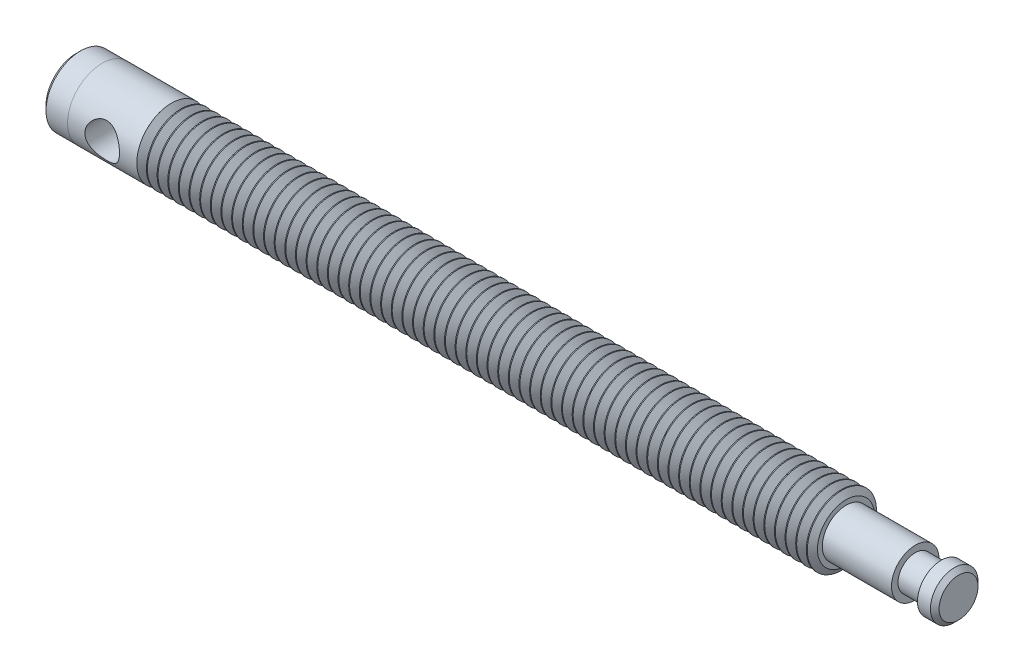
SolidWorks part; units mm, degrees
material "AISI 1015 Steel, Cold Drawn (SS)"
ref_plane "Front Plane" through (0, 0, 0) normal (0, 0, 1) x (1, 0, 0)
ref_plane "Top Plane" through (0, 0, 0) normal (0, 1, 0) x (1, 0, 0)
ref_plane "Right Plane" through (0, 0, 0) normal (1, 0, 0) x (0, 0, -1)
sketch "Sketch1" plane through (0, 0, 0) normal (1, 0, 0) x (0, 0, -1)
  circle A0 centre (0, 0) radius 6.35
  dimension "D1" = 12.7
extrude "Extrude1" add sketch "Sketch1" along normal blind 123.825
sketch "Sketch2" plane through (0, 0, 0) normal (0, 0, 1) x (1, 0, 0)
  line L0 (-0.0003, 6.35) -> (0.889, 5.08)
  line L1 (0.889, 5.08) -> (1.7783, 6.35)
  line L2 (1.7783, 6.35) -> (1.7783, 7.9375)
  line L3 (1.7783, 7.9375) -> (-0.0003, 7.9375)
  line L4 (-0.0003, 7.9375) -> (-0.0003, 6.35)
  line L5 (123.825, 0) -> (0, 0) construction
  line L6 (0, 0) -> (50.8, 0) construction
  dimension "D1" = 55
  dimension "D2" = 70
  dimension "D3" = 15.875
  dimension "D4" = 1.27
  dimension "D5" = 12.7
  dimension "D6" = 0.889
revolve "Cut-Revolve1" cut sketch "Sketch2" angle 360 about L6
pattern_linear "LPattern2" count 64 spacing 1.9533 along (1, 0, 0) of "Cut-Revolve1"
sketch "Sketch3" plane through (123.825, 0, 0) normal (1, 0, 0) x (0, 0, -1)
  circle A0 centre (0, 0) radius 4.3656
  dimension "D1" = 8.7312
extrude "Extrude2" add sketch "Sketch3" along normal blind 12.7
sketch "Sketch4" plane through (136.525, 0, 0) normal (1, 0, 0) x (0, 0, -1)
  circle A0 centre (0, 0) radius 3.175
  dimension "D1" = 6.35
extrude "Extrude3" add sketch "Sketch4" along normal blind 4.7625
sketch "Sketch5" plane through (141.2875, 0, 0) normal (1, 0, 0) x (0, 0, -1)
  circle A0 centre (0, 0) radius 4.3656
  dimension "D1" = 8.7312
extrude "Extrude4" add sketch "Sketch5" along normal blind 3.175
chamfer "Chamfer1" distance 0.7937 angle 45 1 edges at (144.4625, 0, -4.3656)
sketch "Sketch6" plane through (0, 0, 0) normal (-1, 0, 0) x (0, 0, 1)
  circle A0 centre (0, 0) radius 6.35
  dimension "D1" = 12.7
extrude "Extrude5" add sketch "Sketch6" along normal blind 12.7 separate body
sketch "Sketch7" plane through (-12.7, 0, 0) normal (-1, 0, 0) x (0, 0, 1)
  circle A0 centre (0, 0) radius 6.3373
  dimension "D1" = 12.6746
extrude "Extrude6" add sketch "Sketch7" along normal blind 4.7625
chamfer "Chamfer2" distance 0.7937 angle 45 1 edges at (-17.4625, 0, 6.3373)
sketch "Sketch8" plane through (0, 0, 0) normal (0, 0, 1) x (1, 0, 0)
  line L0 (-17.4625, 5.5436) -> (-17.4625, -5.5436) construction
  circle A0 centre (-6.35, 0) radius 3.175
  dimension "D1" = 6.35
  dimension "D2" = 11.1125
extrude "Cut-Extrude1" cut sketch "Sketch8" against normal through all and the other way through all
